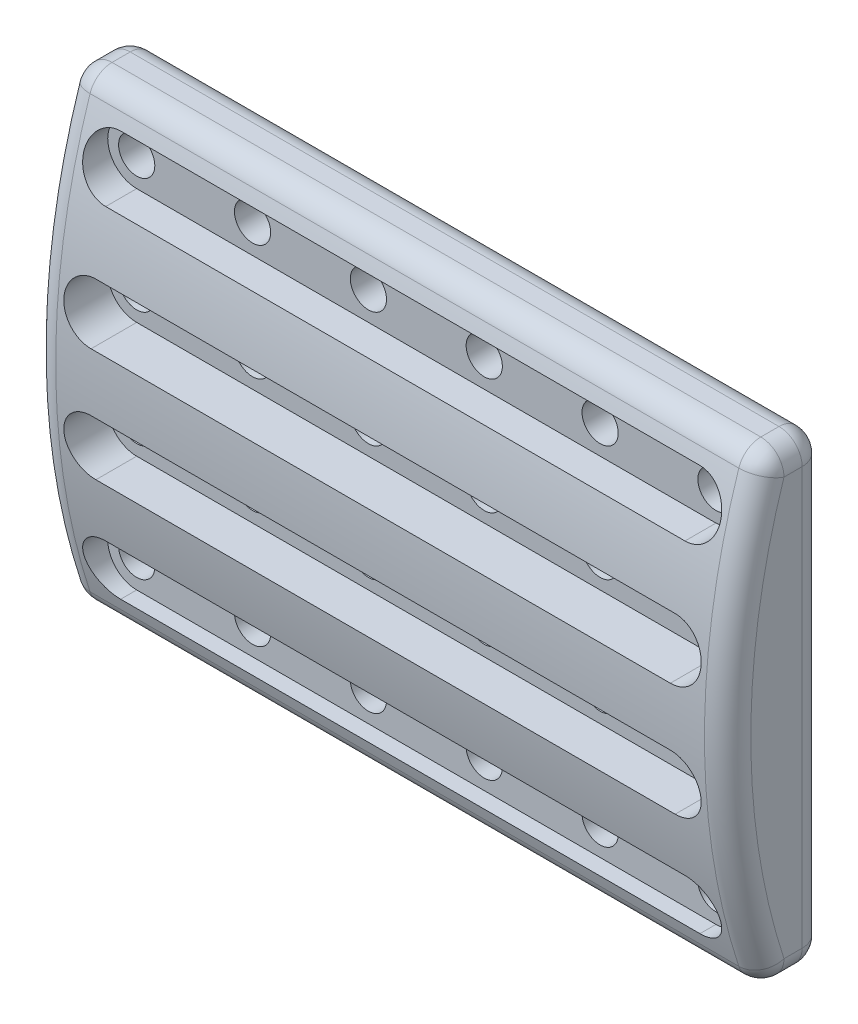
SolidWorks part; units mm, degrees
ref_plane "Front Plane" through (0, 0, 0) normal (0, 0, 1) x (1, 0, 0)
ref_plane "Top Plane" through (0, 0, 0) normal (0, 1, 0) x (1, 0, 0)
ref_plane "Right Plane" through (0, 0, 0) normal (1, 0, 0) x (0, 0, -1)
sketch "Sketch3" plane through (0, 0, 0) normal (1, 0, 0) x (0, 0, -1)
  line L0 (0, 0) -> (0, 50.8)
  line L2 (1.8191, 50.8) -> (3.81, 50.8)
  line L3 (0, 50.8) -> (0, 0)
  line L4 (1.8191, 0) -> (3.81, 0)
  line L5 (6.35, 48.26) -> (6.35, 2.54)
  arc A0 (-0.5955, 49.0483) -> (-0.5955, 1.7517) centre (71.842, 25.4) ccw
  arc A1 (6.35, 48.26) -> (3.81, 50.8) centre (3.81, 48.26) ccw
  arc A2 (6.35, 2.54) -> (3.81, 0) centre (3.81, 2.54) cw
  arc A3 (1.8191, 0) -> (-0.5955, 1.7517) centre (1.8191, 2.54) cw
  arc A4 (1.8191, 50.8) -> (-0.5955, 49.0483) centre (1.8191, 48.26) ccw
  point P8 (6.35, 50.8)
  dimension "D2" = 76.2
  dimension "D4" = 2.54
  dimension "D1" = 50.8
  dimension "D3" = 6.35
extrude "Boss-Extrude1" add sketch "Sketch3" along normal blind 76.2 contours L3 A4 A0 A3 | L2 A4 L3 A3 L4 A2 L5 A1
fillet "Fillet1" radius 2.54 16 edges at (76.2, 50.3159, -0.3275) (76.2, 50.8, -2.8145) (76.2, 50.0561, -5.6061) (76.2, 25.4, -6.35) (76.2, 0.7439, -5.6061) (76.2, 0, -2.8145) (76.2, 0.4841, -0.3275) (0, 50.3159, -0.3275) (0, 50.8, -2.8145) (0, 50.0561, -5.6061) (0, 25.4, -6.35) (0, 0.7439, -5.6061) (0, 0, -2.8145) (0, 0.4841, -0.3275) (76.2, 25.4, 4.358) (0, 25.4, 4.358)
ref_plane "Plane1" through (0, 0, 4.3688) normal (0, 0, -1) x (-1, 0, 0)
sketch "Sketch5" plane through (0, 0, 4.3688) normal (0, 0, -1) x (-1, 0, 0)
  line L0 (-69.85, 31.75) -> (-69.85, 19.05) construction
  line L1 (-6.35, 47.625) -> (-69.85, 47.625)
  line L2 (-6.35, 41.275) -> (-69.85, 41.275)
  line L3 (-2.54, 25.4) -> (-50002.54, 25.4) construction
  line L4 (-76.2, 48.26) -> (-76.2, 2.54) construction
  line L5 (-44.45, 44.45) -> (-31.75, 44.45) construction
  line L6 (-73.66, 50.8) -> (-2.54, 50.8) construction
  line L7 (-73.66, 49.0483) -> (-2.54, 49.0483) construction
  line L8 (-6.35, 34.925) -> (-69.85, 34.925)
  line L9 (-6.35, 28.575) -> (-69.85, 28.575)
  line L10 (-2.54, 49.0483) -> (-2.54, 1.7517) construction
  line L11 (-6.35, 15.875) -> (-69.85, 15.875)
  line L12 (-6.35, 22.225) -> (-69.85, 22.225)
  line L13 (-6.35, 3.175) -> (-69.85, 3.175)
  line L14 (-6.35, 9.525) -> (-69.85, 9.525)
  arc A0 (-6.35, 41.275) -> (-6.35, 47.625) centre (-6.35, 44.45) ccw
  arc A1 (-69.85, 47.625) -> (-69.85, 41.275) centre (-69.85, 44.45) ccw
  arc A2 (-6.35, 28.575) -> (-6.35, 34.925) centre (-6.35, 31.75) ccw
  arc A3 (-69.85, 34.925) -> (-69.85, 28.575) centre (-69.85, 31.75) ccw
  arc A4 (-6.35, 22.225) -> (-6.35, 15.875) centre (-6.35, 19.05) cw
  arc A5 (-69.85, 15.875) -> (-69.85, 22.225) centre (-69.85, 19.05) cw
  arc A6 (-6.35, 9.525) -> (-6.35, 3.175) centre (-6.35, 6.35) cw
  arc A7 (-69.85, 3.175) -> (-69.85, 9.525) centre (-69.85, 6.35) cw
  point P0 (-69.85, 44.45)
  point P3 (-69.85, 31.75)
  point P4 (-69.85, 19.05)
  point P5 (-76.2, 25.4)
  point P9 (-69.85, 6.35)
  point P10 (-69.85, 25.4)
  point P13 (-57.15, 44.45)
  point P14 (-57.15, 31.75)
  point P15 (-57.15, 19.05)
  point P16 (-57.15, 6.35)
  point P20 (-44.45, 44.45)
  point P21 (-44.45, 31.75)
  point P22 (-44.45, 19.05)
  point P23 (-44.45, 6.35)
  point P27 (-31.75, 44.45)
  point P28 (-31.75, 31.75)
  point P29 (-31.75, 19.05)
  point P30 (-31.75, 6.35)
  point P34 (-19.05, 44.45)
  point P35 (-19.05, 31.75)
  point P36 (-19.05, 19.05)
  point P37 (-19.05, 6.35)
  point P40 (12.1889, 46.004)
  point P41 (-6.35, 44.45)
  point P42 (-6.35, 31.75)
  point P43 (-6.35, 19.05)
  point P44 (-6.35, 6.35)
  point P53 (-38.1, 50.8)
  point P54 (-38.1, 44.45)
  point P63 (-2.54, 25.4)
  dimension "D2" = 6.35
  dimension "D3" = 6.35
  dimension "D7" = 6.35
  dimension "D8" = 6.35
  dimension "D1" = 4
  dimension "D4" = 12.7
  dimension "D5" = 6
  dimension "D6" = 12.7
extrude "Cut-Extrude1" cut sketch "Sketch5" along normal blind 5.08
sketch "Sketch13" plane through (0, 0, -0.7112) normal (0, 0, 1) x (1, 0, 0)
  line L0 (73.66, 50.8) -> (2.54, 50.8) construction
  line L1 (0, 48.26) -> (0, 2.54) construction
  point P0 (6.35, 44.45)
  point P7 (19.05, 44.45)
  point P8 (31.75, 44.45)
  point P9 (44.45, 44.45)
  point P10 (57.15, 44.45)
  point P11 (69.85, 44.45)
  point P12 (6.35, 31.75)
  point P13 (19.05, 31.75)
  point P14 (31.75, 31.75)
  point P15 (44.45, 31.75)
  point P16 (57.15, 31.75)
  point P17 (69.85, 31.75)
  point P18 (6.35, 19.05)
  point P19 (19.05, 19.05)
  point P20 (31.75, 19.05)
  point P21 (44.45, 19.05)
  point P22 (57.15, 19.05)
  point P23 (69.85, 19.05)
  point P24 (6.35, 6.35)
  point P25 (19.05, 6.35)
  point P26 (31.75, 6.35)
  point P27 (44.45, 6.35)
  point P28 (57.15, 6.35)
  point P29 (69.85, 6.35)
  dimension "D1" = 6.35
  dimension "D2" = 6.35
  dimension "D4" = 12.7
  dimension "D6" = 12.7
  dimension "D3" = 6
  dimension "D5" = 4
hole_wizard "5/32 (0.15625) Diameter Hole1" positions "3DSketch6" profile "Sketch14" hole size "5/32" standard "ANSI Inch" end condition through all
sketch3d "3DSketch6"
  point P0 (6.35, 44.45, -0.7112)
  point P3 (19.05, 44.45, -0.7112)
  point P6 (31.75, 44.45, -0.7112)
  point P9 (44.45, 44.45, -0.7112)
  point P12 (57.15, 44.45, -0.7112)
  point P15 (69.85, 44.45, -0.7112)
  point P18 (6.35, 31.75, -0.7112)
  point P21 (19.05, 31.75, -0.7112)
  point P24 (31.75, 31.75, -0.7112)
  point P27 (44.45, 31.75, -0.7112)
  point P30 (57.15, 31.75, -0.7112)
  point P33 (69.85, 31.75, -0.7112)
  point P36 (69.85, 19.05, -0.7112)
  point P39 (57.15, 19.05, -0.7112)
  point P42 (44.45, 19.05, -0.7112)
  point P45 (31.75, 19.05, -0.7112)
  point P48 (19.05, 19.05, -0.7112)
  point P51 (6.35, 19.05, -0.7112)
  point P54 (6.35, 6.35, -0.7112)
  point P57 (19.05, 6.35, -0.7112)
  point P60 (31.75, 6.35, -0.7112)
  point P63 (44.45, 6.35, -0.7112)
  point P66 (57.15, 6.35, -0.7112)
  point P69 (69.85, 6.35, -0.7112)
sketch "Sketch14" plane through (6.35, 44.45, -0.7112) normal (1, 0, 0) x (0, -1, 0)
  line L0 (0, 0) -> (0, 5.6388)
  line L1 (0, 5.6388) -> (1.9844, 5.6388)
  line L2 (1.9844, 5.6388) -> (1.9844, 0)
  line L5 (1.9844, 0) -> (0, 0)
  line L11 (0, -6.35) -> (0, 107.95) construction
  dimension "Thru Hole Dia." = 3.9688
  dimension "Thru Hole Depth" = 5.6388
